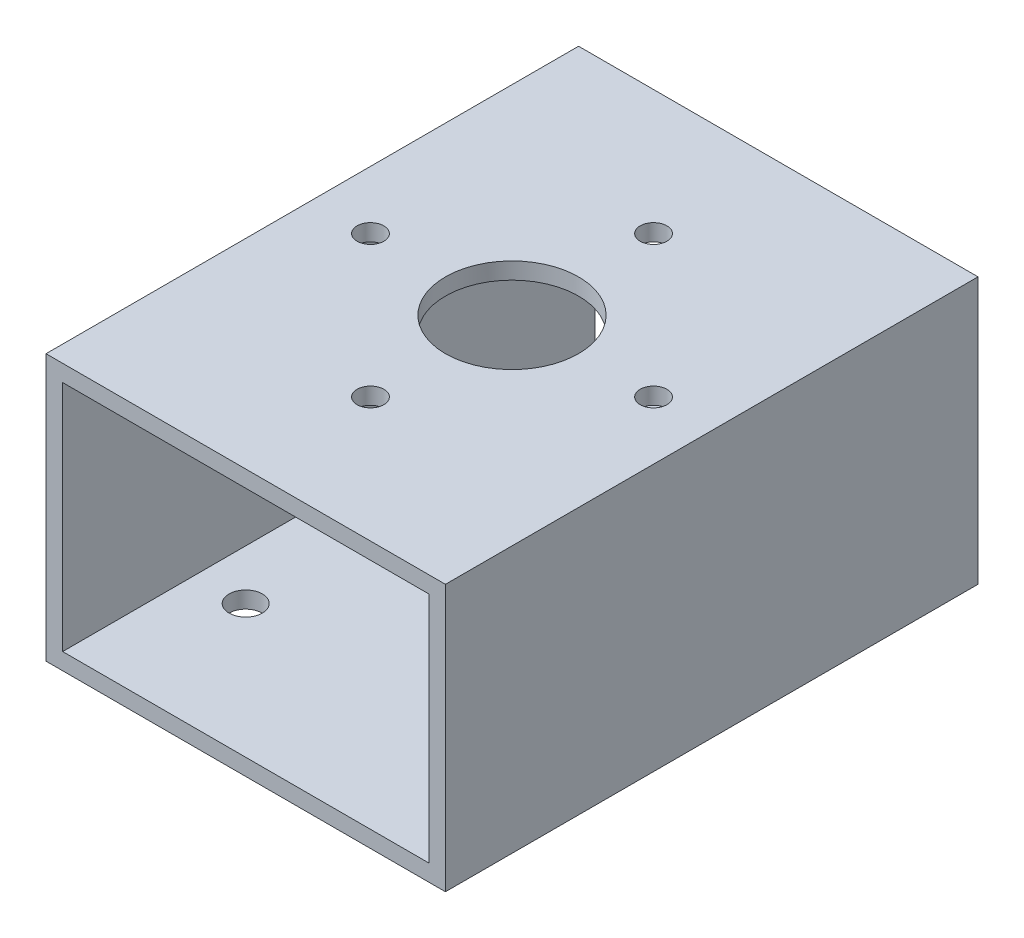
SolidWorks part; units mm, degrees
material "6061-T6 (SS)"
ref_plane "Front Plane" through (0, 0, 0) normal (0, 0, 1) x (1, 0, 0)
ref_plane "Top Plane" through (0, 0, 0) normal (0, 1, 0) x (1, 0, 0)
ref_plane "Right Plane" through (0, 0, 0) normal (1, 0, 0) x (0, 0, -1)
sketch "Sketch1" plane through (0, 0, 0) normal (0, 0, 1) x (1, 0, 0)
  line L0 (-34.925, 22.225) -> (34.925, 22.225)
  line L1 (-38.1, -25.4) -> (38.1, -25.4)
  line L2 (-38.1, -25.4) -> (-38.1, 25.4)
  line L3 (-38.1, 25.4) -> (38.1, 25.4)
  line L4 (38.1, -25.4) -> (38.1, 25.4)
  line L5 (-38.1, -25.4) -> (38.1, 25.4) construction
  line L6 (-38.1, 25.4) -> (38.1, -25.4) construction
  line L7 (34.925, -22.225) -> (34.925, 22.225)
  line L8 (-34.925, -22.225) -> (34.925, -22.225)
  line L9 (-34.925, -22.225) -> (-34.925, 22.225)
  point P0 (0, 0)
  dimension "D1" = 76.2
  dimension "D2" = 50.8
  dimension "D3" = 3.175
extrude "Boss-Extrude1" add sketch "Sketch1" along normal blind 101.6
sketch "Sketch2" plane through (0, 25.4, 0) normal (0, 1, 0) x (1, 0, 0)
  line L0 (0, 0) -> (0, -101.6) construction
  line L1 (38.1, -101.6) -> (-38.1, -101.6) construction
  line L2 (-38.1, -50.8) -> (38.1, -50.8) construction
  line L3 (-38.1, -101.6) -> (-38.1, 0) construction
  line L4 (38.1, -101.6) -> (38.1, 0) construction
  point P11 (0, -23.7998)
  point P12 (0, -50.8)
  point P16 (27.0002, -50.8)
  point P17 (0, -77.8002)
  point P18 (-27.0002, -50.8)
  point P19 (0, -50.8)
  dimension "D1" = 27.0002
  dimension "D2" = 4
hole_wizard "#7 (0.201) Diameter Hole1" positions "Sketch3" profile "Sketch4" hole size "#7" standard "ANSI Inch"
sketch "Sketch3" plane through (0, 25.4, 0) normal (0, 1, 0) x (1, 0, 0)
  point P0 (-27.0002, -50.8)
  point P3 (0, -23.7998)
  point P6 (27.0002, -50.8)
  point P9 (0, -77.8002)
sketch "Sketch4" plane through (-27.0002, 25.4, 50.8) normal (1, 0, 0) x (0, 0, 1)
  line L0 (0, 0) -> (0, 4.7078)
  line L1 (0, 4.7078) -> (2.5527, 3.174)
  line L2 (2.5527, 3.174) -> (2.5527, 0)
  line L5 (2.5527, 0) -> (0, 0)
  line L10 (0, 4.7078) -> (-2.5527, 3.174) construction
  line L11 (0, -6.35) -> (0, 107.95) construction
  dimension "Hole Dia." = 5.1054
  dimension "Hole Depth" = 3.174
  dimension "Drill Angle" = 118
sketch "Sketch5" plane through (0, -25.4, 0) normal (0, -1, 0) x (1, 0, 0)
  line L0 (-25.4, 101.6) -> (-25.4, 0) construction
  line L1 (-34.925, 101.6) -> (34.925, 101.6) construction
  line L2 (-38.1, 0) -> (38.1, 0) construction
  line L3 (-38.1, 101.6) -> (-38.1, 0) construction
  line L4 (-38.1, 50.8) -> (38.1, 50.8) construction
  line L5 (0, 101.6) -> (0, 0) construction
  point P8 (-25.4, 76.2)
  point P10 (-25.4, 25.4)
  point P16 (25.4, 25.4)
  point P17 (25.4, 76.2)
  dimension "D1" = 12.7
  dimension "D2" = 25.4
  dimension "D3" = 50.8
hole_wizard "1/4 (0.25) Diameter Hole1" positions "Sketch6" profile "Sketch7" hole size "1/4" standard "ANSI Inch"
sketch "Sketch6" plane through (0, -25.4, 0) normal (0, -1, 0) x (-1, 0, 0)
  point P0 (25.4, -25.4)
  point P3 (25.4, -76.2)
  point P6 (-25.4, -76.2)
  point P9 (-25.4, -25.4)
sketch "Sketch7" plane through (-25.4, -25.4, 25.4) normal (1, 0, 0) x (0, 0, -1)
  line L0 (0, 0) -> (0, 3.175)
  line L1 (0, 3.175) -> (3.175, 3.175)
  line L2 (3.175, 3.175) -> (3.175, 0)
  line L5 (3.175, 0) -> (0, 0)
  line L11 (0, -6.35) -> (0, 107.95) construction
  dimension "Thru Hole Dia." = 6.35
  dimension "Thru Hole Depth" = 3.175
sketch "Sketch8" plane through (0, 25.4, 0) normal (0, 1, 0) x (1, 0, 0)
  line L0 (-38.1, -50.8) -> (38.1, -50.8) construction
  circle A0 centre (0, -50.8) radius 12.7
  dimension "D1" = 25.4
extrude "Cut-Extrude1" cut sketch "Sketch8" against normal up to next
